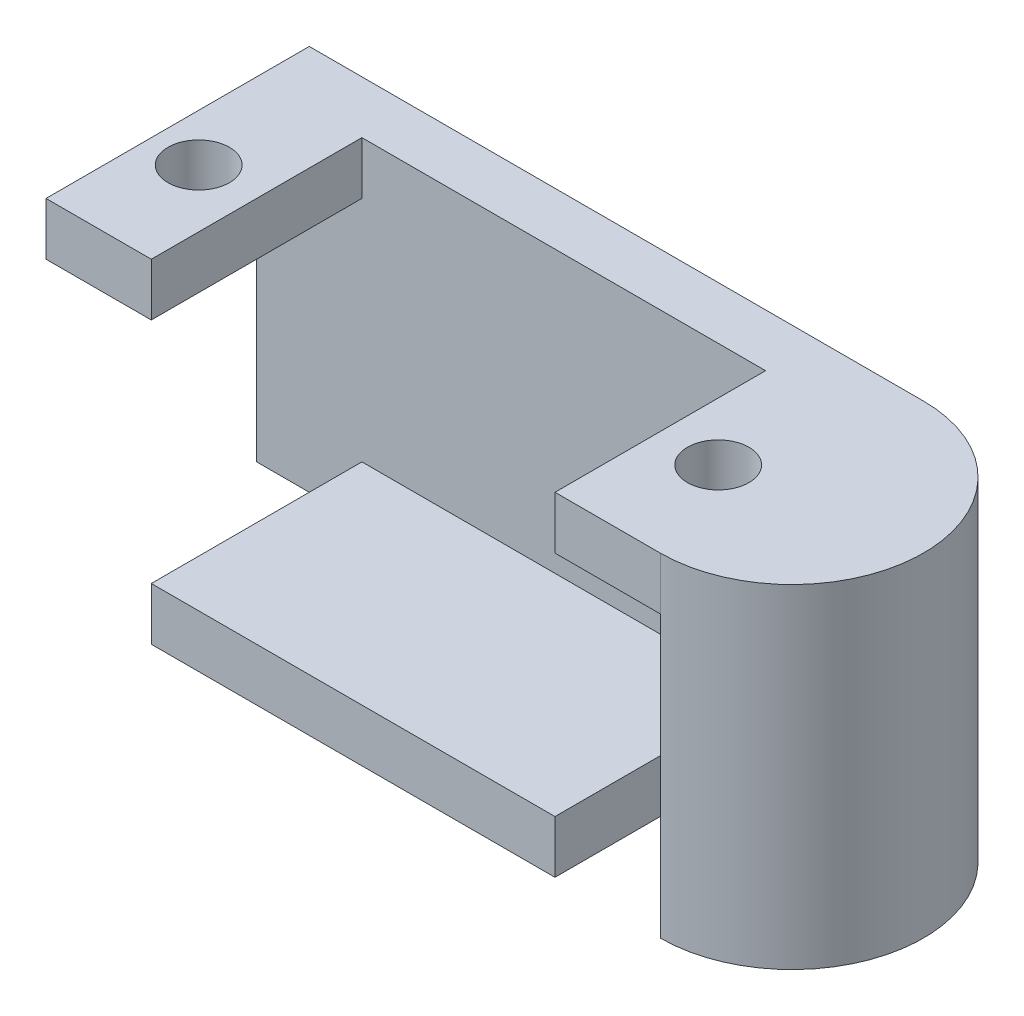
SolidWorks part; units mm, degrees
ref_plane "Plan de face" through (0, 0, 0) normal (0, 0, 1) x (1, 0, 0)
ref_plane "Plan de dessus" through (0, 0, 0) normal (0, 1, 0) x (1, 0, 0)
ref_plane "Plan de droite" through (0, 0, 0) normal (1, 0, 0) x (0, 0, -1)
sketch "Esquisse1" plane through (0, 0, 0) normal (0, 1, 0) x (1, 0, 0)
  line L1 (0, 0) -> (35, 0)
  line L2 (0, 0) -> (0, 15)
  line L3 (0, 15) -> (35, 15)
  arc A0 (35, 0) -> (35, 15) centre (35, 7.5) ccw
  dimension "D1" = 15
  dimension "D2" = 35
extrude "Boss.-Extru.1" add sketch "Esquisse1" along normal blind 19
sketch "Esquisse3" plane through (0, 0, 0) normal (0, 0, 1) x (1, 0, 0)
  line L1 (6, 19) -> (29, 19)
  line L2 (6, 19) -> (6, 16)
  line L3 (6, 3) -> (29, 3)
  line L4 (29, 19) -> (29, 16)
  line L6 (29, 16) -> (35, 16)
  line L7 (0, 19) -> (35, 19) construction
  line L8 (35, 3.1448) -> (35, 0)
  line L9 (35, 16) -> (35, 3.1448)
  line L10 (35, 0) -> (29, 0)
  line L11 (0, 19) -> (0, 0) construction
  line L13 (6, 16) -> (0, 16)
  line L14 (0, 3.8248) -> (0, 16)
  line L16 (29, 0) -> (29, 3)
  line L17 (6, 3) -> (6, 0)
  line L18 (6, 0) -> (0, 0)
  line L19 (0, 0) -> (0, 3.8248)
  dimension "D1" = 23
  dimension "D2" = 6
  dimension "D3" = 6
  dimension "D4" = 3
  dimension "D5" = 3
  dimension "D6" = 3
  dimension "D8" = 23
  dimension "D9" = 6
extrude "Enlèv. mat.-Extru.2" cut sketch "Esquisse3" against normal blind 12
sketch "Esquisse4" plane through (0, 19, 0) normal (0, 1, 0) x (1, 0, 0)
  line L0 (6, 12) -> (6, 0) construction
  line L1 (0, 0) -> (6, 0) construction
  line L2 (29, 0) -> (35, 0) construction
  line L3 (29, 12) -> (29, 0) construction
  circle A0 centre (2.7, 6) radius 1.75
  circle A1 centre (32.3, 6) radius 1.75
  dimension "D1" = 3.5
  dimension "D2" = 3.5
  dimension "D3" = 3.3
  dimension "D4" = 6
  dimension "D6" = 3.3
  dimension "D5" = 6
extrude "Enlèv. mat.-Extru.3" cut sketch "Esquisse4" against normal blind 12
sketch "Esquisse5" plane through (0, 0, 0) normal (0, -1, 0) x (1, 0, 0)
  line L0 (6, 0) -> (29, 0) construction
  line L1 (6, -12) -> (6, 0) construction
  circle A0 centre (12, -6) radius 1.25
  dimension "D1" = 2.5
  dimension "D2" = 6
  dimension "D3" = 6
extrude "Boss.-Extru.2" add sketch "Esquisse5" along normal blind 3
